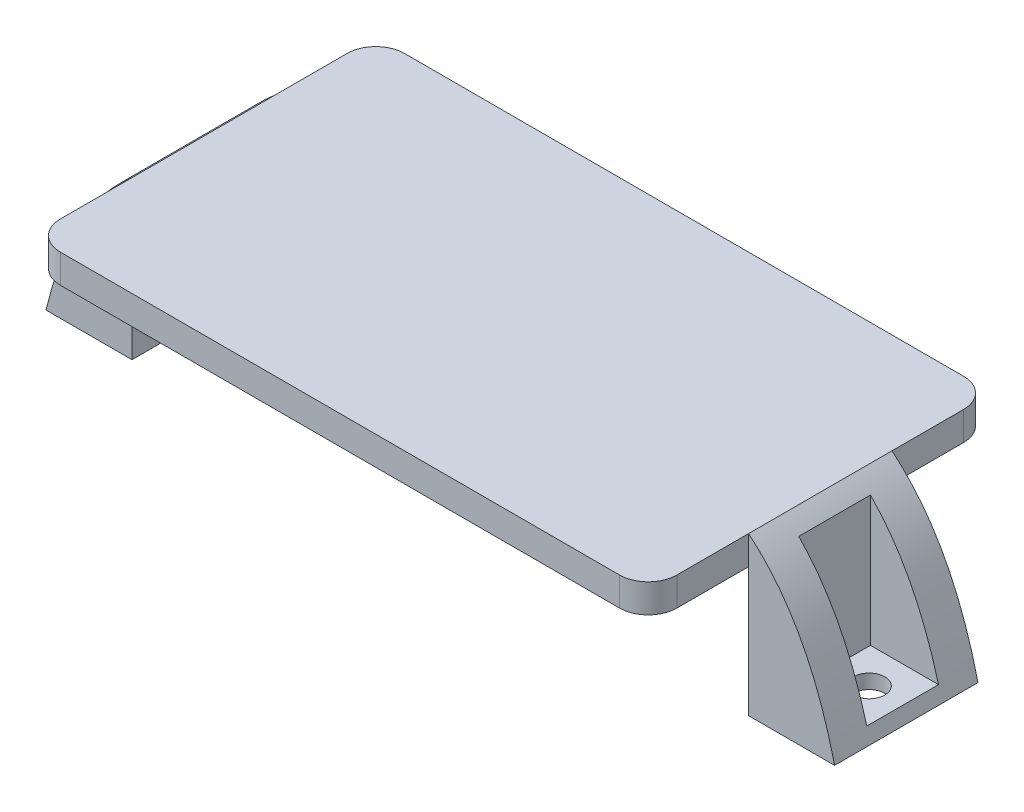
SolidWorks part; units mm, degrees
ref_plane "Front Plane" through (0, 0, 0) normal (0, 0, 1) x (1, 0, 0)
ref_plane "Top Plane" through (0, 0, 0) normal (0, 1, 0) x (1, 0, 0)
ref_plane "Right Plane" through (0, 0, 0) normal (1, 0, 0) x (0, 0, -1)
sketch "Sketch1" plane through (0, 0, 0) normal (0, 1, 0) x (1, 0, 0)
  line L1 (-27.305, -15.24) -> (27.305, -15.24)
  line L2 (-27.305, -15.24) -> (-27.305, 15.24)
  line L3 (-27.305, 15.24) -> (27.305, 15.24)
  line L4 (27.305, -15.24) -> (27.305, 15.24)
  line L5 (-27.305, -15.24) -> (27.305, 15.24) construction
  line L6 (-27.305, 15.24) -> (27.305, -15.24) construction
  point P0 (0, 0)
  dimension "D1" = 54.61
  dimension "D2" = 30.48
extrude "Boss-Extrude1" add sketch "Sketch1" against normal blind 2.54
fillet "Fillet1" radius 2.54 4 edges at (-27.305, -1.27, -15.24) (-27.305, -1.27, 15.24) (27.305, -1.27, 15.24) (27.305, -1.27, -15.24)
sketch "Sketch2" plane through (0, 0, 0) normal (0, 0, 1) x (1, 0, 0)
  line L0 (27.305, 0) -> (27.305, -13.97)
  line L1 (27.305, -13.97) -> (34.925, -13.97)
  spline S0 degree 2 poles (34.925, -13.97) (28.724, 11.9855) (0, 0) knots 0 0 0 1 1 1
  dimension "D1" = 7.62
extrude "Boss-Extrude2" add sketch "Sketch2" along normal blind 6.35 and the other way blind 6.35 contours L1 S0 L0
sketch "Sketch3" plane through (0, 0, 0) normal (0, 1, 0) x (1, 0, 0)
  line L1 (34.925, -3.175) -> (28.575, -3.175)
  line L2 (34.925, -3.175) -> (34.925, 3.175)
  line L3 (34.925, 3.175) -> (28.575, 3.175)
  line L4 (28.575, -3.175) -> (28.575, 3.175)
  dimension "D1" = 6.35
  dimension "D2" = 6.35
extrude "Cut-Extrude1" cut sketch "Sketch3" against normal blind 12.7
sketch "Sketch4" plane through (0, -13.97, 0) normal (0, -1, 0) x (-1, 0, 0)
  circle A0 centre (-31.623, 0) radius 1.397
extrude "Cut-Extrude2" cut sketch "Sketch4" against normal through all
mirror "Mirror1" about plane through (0, 0, 0) normal (1, 0, 0) of "Cut-Extrude2", "Cut-Extrude1", "Boss-Extrude2"
